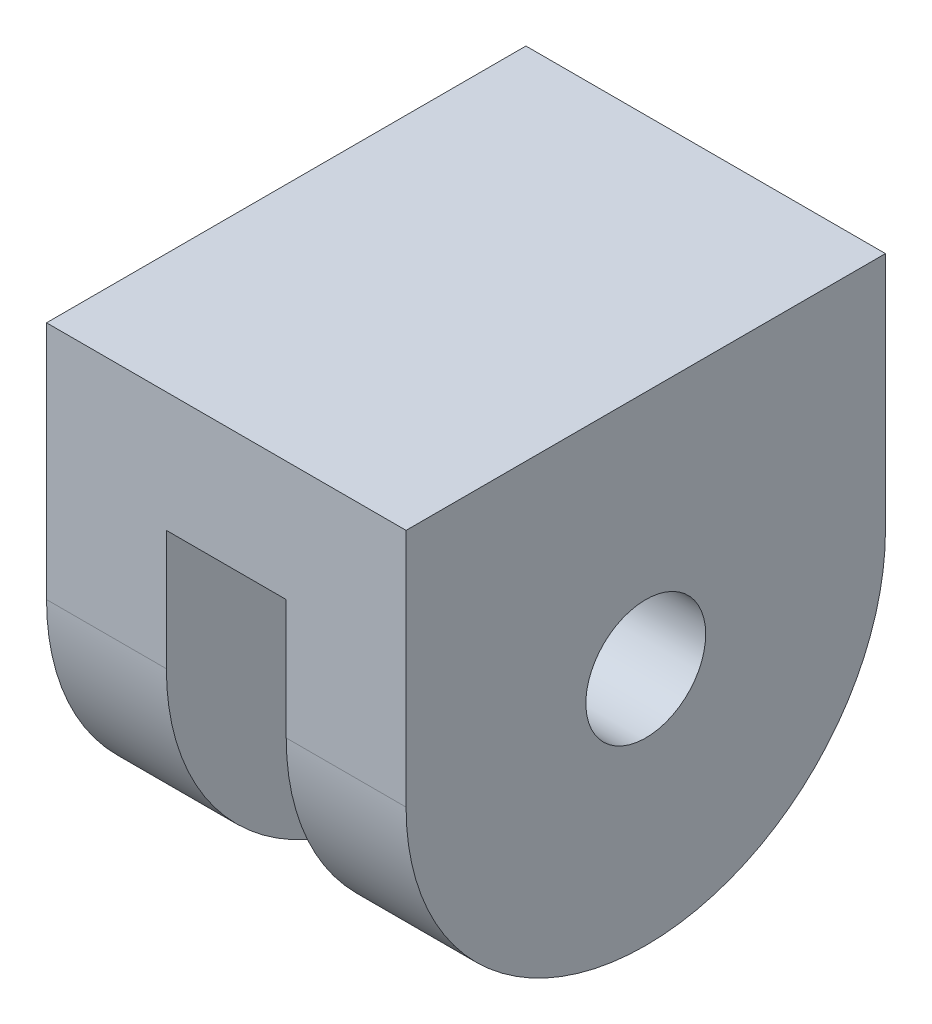
SolidWorks part; units mm, degrees
material "PF"
ref_plane "Front Plane" through (0, 0, 0) normal (0, 0, 1) x (1, 0, 0)
ref_plane "Top Plane" through (0, 0, 0) normal (0, 1, 0) x (1, 0, 0)
ref_plane "Right Plane" through (0, 0, 0) normal (1, 0, 0) x (0, 0, -1)
sketch "Sketch1" plane through (0, 0, 0) normal (1, 0, 0) x (0, 0, -1)
  line L0 (0, 0) -> (0, -12.7) construction
  line L1 (12.7, 0) -> (12.7, -12.7)
  line L2 (-12.7, 0) -> (-12.7, -12.7)
  line L3 (-12.7, 0) -> (12.7, 0)
  arc A1 (-12.7, -12.7) -> (12.7, -12.7) centre (0, -12.7) ccw
  point P9 (0, -25.4)
  dimension "D1" = 25.4
  dimension "D2" = 25.4
  dimension "D3" = 12.7
extrude "mount" add sketch "Sketch1" along normal mid plane 19.05
sketch "Sketch2" plane through (0, 0, 0) normal (0, 0, 1) x (1, 0, 0)
  line L0 (-9.525, -25.4) -> (9.525, -25.4) construction
  line L1 (-3.175, -25.4) -> (3.175, -25.4)
  line L2 (-3.175, -25.4) -> (-3.175, -6.35)
  line L3 (-3.175, -6.35) -> (3.175, -6.35)
  line L4 (3.175, -25.4) -> (3.175, -6.35)
  line L5 (-3.175, -25.4) -> (3.175, -6.35) construction
  line L6 (-3.175, -6.35) -> (3.175, -25.4) construction
  line L7 (9.525, 0) -> (-9.525, 0) construction
  point P0 (0, -15.875)
  dimension "D1" = 6.35
  dimension "D2" = 6.35
extrude "center cutout for rib" cut sketch "Sketch2" against normal through all and the other way through all
sketch "Sketch3" plane through (0, 0, 0) normal (1, 0, 0) x (0, 0, -1)
  circle A0 centre (0, -12.7) radius 3.175
  dimension "D1" = 6.35
extrude "pin hole" cut sketch "Sketch3" against normal through all and the other way through all
